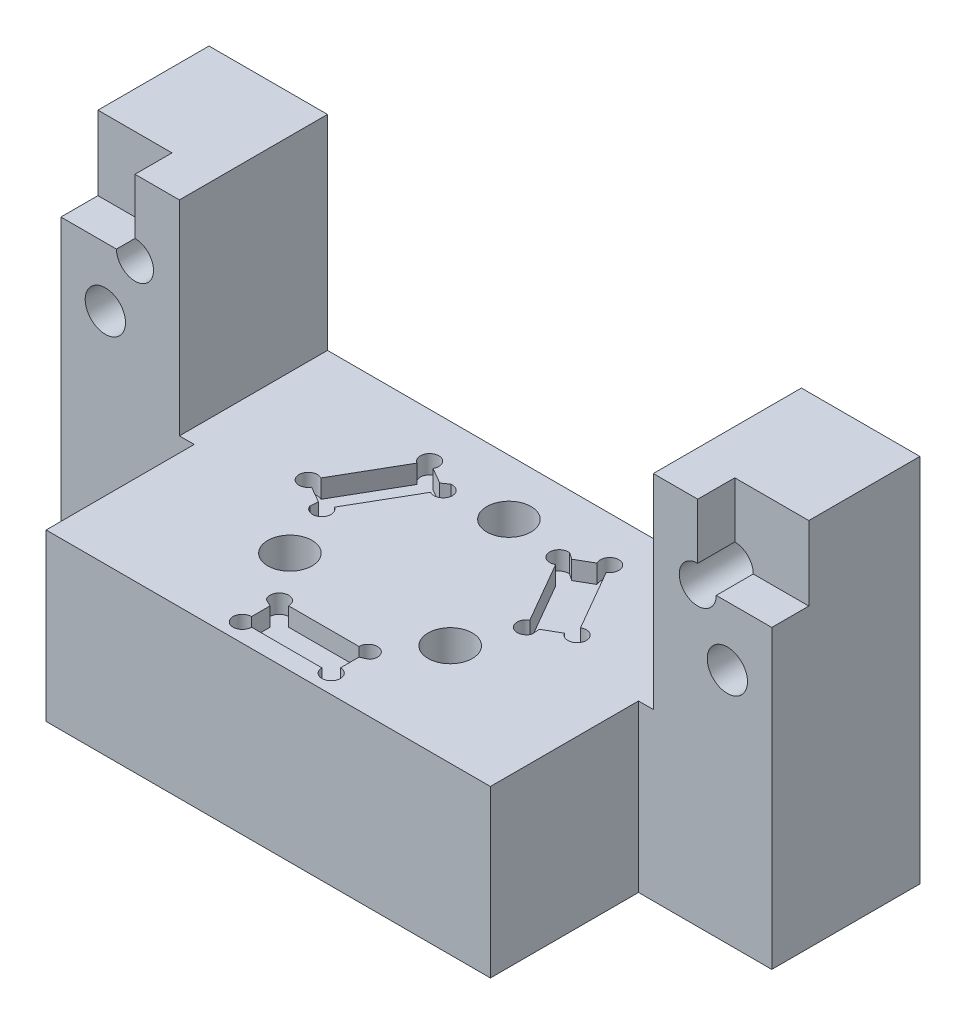
SolidWorks part; units mm, degrees
material "6061 Alloy"
ref_plane "Front Plane" through (0, 0, 0) normal (0, 0, 1) x (1, 0, 0)
ref_plane "Top Plane" through (0, 0, 0) normal (0, 1, 0) x (1, 0, 0)
ref_plane "Right Plane" through (0, 0, 0) normal (1, 0, 0) x (0, 0, -1)
sketch "Sketch1" plane through (0, 0, 0) normal (0, 0, 1) x (1, 0, 0)
  line L1 (-30.48, 15.875) -> (30.48, 15.875)
  line L2 (-30.48, 15.875) -> (-30.48, -15.875)
  line L3 (-30.48, -15.875) -> (30.48, -15.875)
  line L4 (30.48, 15.875) -> (30.48, -15.875)
  dimension "D1" = 30.48
  dimension "D2" = 30.48
  dimension "D3" = 15.875
  dimension "D4" = 15.875
extrude "Boss-Extrude1" add sketch "Sketch1" along normal mid plane 25.4
sketch "Sketch4" plane through (0, 0, 12.7) normal (0, 0, 1) x (1, 0, 0)
  line L0 (30.48, 15.875) -> (-30.48, 15.875) construction
  line L1 (-20.32, 15.875) -> (20.32, 15.875)
  line L2 (-20.32, 15.875) -> (-20.32, -1.651)
  line L3 (-20.32, -1.651) -> (20.32, -1.651)
  line L4 (20.32, 15.875) -> (20.32, -1.651)
  dimension "D1" = 40.64
  dimension "D2" = 20.32
  dimension "D3" = 17.526
extrude "Cut-Extrude2" cut sketch "Sketch4" against normal up to next
sketch "Sketch5" plane through (0, 0, 12.7) normal (0, 0, 1) x (1, 0, 0)
  line L0 (-30.48, -15.875) -> (30.48, -15.875) construction
  line L1 (30.48, 15.875) -> (19.05, 15.875)
  line L2 (30.48, 15.875) -> (30.48, -15.875)
  line L3 (30.48, -15.875) -> (19.05, -15.875)
  line L4 (19.05, 15.875) -> (19.05, -15.875)
  dimension "D1" = 11.43
  dimension "D2" = 31.75
extrude "Cut-Extrude3" cut sketch "Sketch5" against normal blind 12.7
mirror "Mirror2" about plane through (0, 0, 0) normal (1, 0, 0) of "Cut-Extrude3"
sketch "Sketch6" plane through (0, 0, 0) normal (0, 0, 1) x (1, 0, 0)
  line L1 (30.48, 15.875) -> (24.13, 15.875)
  line L2 (30.48, 15.875) -> (30.48, 9.525)
  line L3 (30.48, 9.525) -> (24.13, 9.525)
  line L4 (24.13, 15.875) -> (24.13, 9.525)
  dimension "D1" = 6.35
  dimension "D2" = 6.35
extrude "Cut-Extrude4" cut sketch "Sketch6" against normal blind 3.175
sketch "Sketch7" plane through (0, 0, 0) normal (0, 0, 1) x (1, 0, 0)
  circle A0 centre (24.13, 9.525) radius 1.5875
extrude "Cut-Extrude5" cut sketch "Sketch7" against normal blind 6.35
hole_wizard "#8-32 Tapped Hole1" positions "Sketch9" profile "Sketch8" tap size "#8-32" standard "ANSI Inch" end condition up to next
sketch "Sketch9" plane through (0, 0, 0) normal (0, 0, 1) x (1, 0, 0)
  line L0 (30.48, -15.875) -> (30.48, 9.525) construction
  line L1 (24.13, 15.875) -> (20.32, 15.875) construction
  point P0 (26.67, 4.445)
  dimension "D1" = 3.81
  dimension "D2" = 11.43
sketch "Sketch8" plane through (26.67, 4.445, 0) normal (1, 0, 0) x (0, -1, 0)
  line L0 (0, 0) -> (0, 12.701)
  line L1 (0, 12.701) -> (1.7272, 12.701)
  line L2 (1.7272, 12.701) -> (1.7272, 0)
  line L5 (1.7272, 0) -> (0, 0)
  line L11 (0, -6.35) -> (0, 107.95) construction
  dimension "Thru Tap Drill Dia." = 3.4544
  dimension "Thru Tap Drill Depth" = 12.701
cosmetic thread "Hole Thread1" parameters "D2"=4.1656
sketch "Sketch10" plane through (0, -1.651, 0) normal (0, 1, 0) x (1, 0, 0)
  circle A0 centre (5.08, 8.89) radius 2.2352
  circle A1 centre (5.08, -8.89) radius 2.2352
  circle A2 centre (-10.16, 0) radius 2.2352
  dimension "D1" = 5.08
  dimension "D2" = 8.89
  dimension "D3" = 8.89
  dimension "D4" = 10.16
extrude "Cut-Extrude6" [suppressed] cut sketch "Sketch10" against normal up to next
mirror "Mirror3" about plane through (0, 0, 0) normal (1, 0, 0) of "#8-32 Tapped Hole1", "Cut-Extrude5", "Cut-Extrude4"
sketch "Sketch13" plane through (0, -1.651, 0) normal (0, 1, 0) x (1, 0, 0)
  line L1 (-3.81, -11.1125) -> (3.81, -11.1125)
  line L2 (-3.81, -11.1125) -> (-3.81, -7.9375)
  line L3 (-3.81, -7.9375) -> (3.81, -7.9375)
  line L4 (3.81, -11.1125) -> (3.81, -7.9375)
  line L5 (-3.81, -11.1125) -> (3.81, -7.9375) construction
  line L6 (-3.81, -7.9375) -> (3.81, -11.1125) construction
  line L8 (-7.7187, 8.8558) -> (-4.9691, 7.2683)
  line L11 (-4.9691, 7.2683) -> (-8.7791, 0.6692)
  line L14 (-4.9691, 7.2683) -> (-11.5287, 2.2567) construction
  line L17 (-7.7187, 8.8558) -> (-8.7791, 0.6692) construction
  line L18 (-11.5287, 2.2567) -> (-8.7791, 0.6692) [skipped]
  line L19 (-4.9691, 7.2683) -> (-8.7791, 0.6692) [skipped]
  line L20 (-7.7187, 8.8558) -> (-4.9691, 7.2683) [skipped]
  line L21 (-7.7187, 8.8558) -> (-11.5287, 2.2567) [skipped]
  line L22 (-7.7187, 8.8558) -> (-8.7791, 0.6692) construction
  line L23 (-4.9691, 7.2683) -> (-11.5287, 2.2567) construction
  line L24 (7.7187, 8.8558) -> (4.9691, 7.2683) [skipped]
  line L25 (8.7791, 0.6692) -> (4.9691, 7.2683) [skipped]
  line L26 (11.5287, 2.2567) -> (8.7791, 0.6692) [skipped]
  line L27 (11.5287, 2.2567) -> (7.7187, 8.8558) [skipped]
  line L28 (8.7791, 0.6692) -> (7.7187, 8.8558) construction
  line L29 (11.5287, 2.2567) -> (4.9691, 7.2683) construction
  line L30 (-7.7187, 8.8558) -> (-11.5287, 2.2567)
  line L31 (-11.5287, 2.2567) -> (-8.7791, 0.6692)
  line L32 (11.5287, 2.2567) -> (8.7791, 0.6692)
  line L33 (8.7791, 0.6692) -> (4.9691, 7.2683)
  line L34 (8.7791, 0.6692) -> (7.7187, 8.8558) construction
  line L35 (11.5287, 2.2567) -> (4.9691, 7.2683) construction
  line L36 (11.5287, 2.2567) -> (7.7187, 8.8558)
  line L37 (7.7187, 8.8558) -> (4.9691, 7.2683)
  circle A0 centre (0, 0) radius 9.525
  circle A1 centre (0, 0) radius 9.525
  circle A2 centre (0, 0) radius 9.525
  circle A3 centre (-3.81, -7.9375) radius 0.7937
  circle A4 centre (-3.81, -11.1125) radius 0.7937
  circle A5 centre (3.81, -11.1125) radius 0.7937
  circle A6 centre (3.81, -7.9375) radius 0.7937
  circle A7 centre (0, 0) radius 9.525
  circle A8 centre (-4.9691, 7.2683) radius 0.7937
  circle A9 centre (-7.7187, 8.8558) radius 0.7937
  circle A10 centre (-11.5287, 2.2567) radius 0.7937
  circle A11 centre (-8.7791, 0.6692) radius 0.7937
  circle A12 centre (0, 0) radius 9.525
  circle A13 centre (8.7791, 0.6692) radius 0.7938
  circle A14 centre (11.5287, 2.2567) radius 0.7937
  circle A15 centre (7.7187, 8.8558) radius 0.7938
  circle A16 centre (4.9691, 7.2683) radius 0.7938
  point P3 (0, -9.525)
  point P12 (-8.2489, 4.7625)
  point P13 (8.2489, 4.7625)
  point P17 (-8.2489, 4.7625)
  point P22 (0, 0)
  point P55 (8.2489, 4.7625)
  point P64 (0, 0)
  dimension "D1" = 3.175
  dimension "D4" = 19.05
  dimension "D6" = 1.5875
  dimension "D7" = 1.5875
  dimension "D8" = 1.5875
  dimension "D9" = 1.5875
  dimension "D2" = 7.62
  dimension "D3" = 3
  dimension "D5" = 3
extrude "Cut-Extrude7" cut sketch "Sketch13" against normal blind 1.5875 contours A6 L3 A3 A2 | A6 A2 A3 L2 A4 L1 A5 L4 | A0 A3 L3 L2 | L3 A3 A2 L2 | L1 A4 L2 | L2 A4 L1 | L4 A5 L1 | L1 A5 L4 | L3 A6 A0 L4 | A0 A6 L3 L4 | A16 A12 A13 L32 A14 L36 A15 L37 | A16 L33 A13 A12 | L32 A14 L36 | L36 A14 L32 | L37 A15 L36 | L36 A15 L37 | L33 A16 A0 L37 | A0 A16 L33 L37 | A0 A13 L33 L32 | L33 A13 A12 L32 | A11 L11 A8 A7 | A11 A7 A8 L8 A9 L30 A10 L31 | A0 A8 L11 L8 | L11 A8 A7 L8 | L11 A11 A0 L31 | A0 A11 L11 L31 | L31 A10 L30 | L30 A10 L31 | L30 A9 L8 | L8 A9 L30
hole_wizard "CBORE for #6 Socket Head Cap Screw1" positions "Sketch14" profile "Sketch15" counterbore size "#6" standard "ANSI Inch" end condition through all
sketch "Sketch14" plane through (0, -15.875, 0) normal (0, -1, 0) x (-1, 0, 0)
  line L0 (30.48, 12.7) -> (-30.48, 12.7) construction
  point P0 (0, 7.9375)
  point P12 (6.8741, -3.9687)
  point P13 (-6.8741, -3.9688)
  dimension "D1" = 4.7625
  dimension "D2" = 3
sketch "Sketch15" plane through (0, -15.875, -7.9375) normal (1, 0, 0) x (0, 0, -1)
  line L0 (0, 0) -> (0, 31.75)
  line L1 (0, 31.75) -> (1.8986, 31.75)
  line L3 (1.8986, 31.75) -> (1.8987, 3.5052)
  line L4 (1.8987, 3.5052) -> (3.5725, 3.5052)
  line L5 (3.5725, 3.5052) -> (3.5725, 0)
  line L7 (3.5725, 0) -> (0, 0)
  line L11 (0, -6.35) -> (0, 107.95) construction
  dimension "Thru Hole Dia." = 3.7973
  dimension "Thru Hole Depth" = 31.75
  dimension "C'Bore Dia." = 7.145
  dimension "C'Bore Depth" = 3.5052
